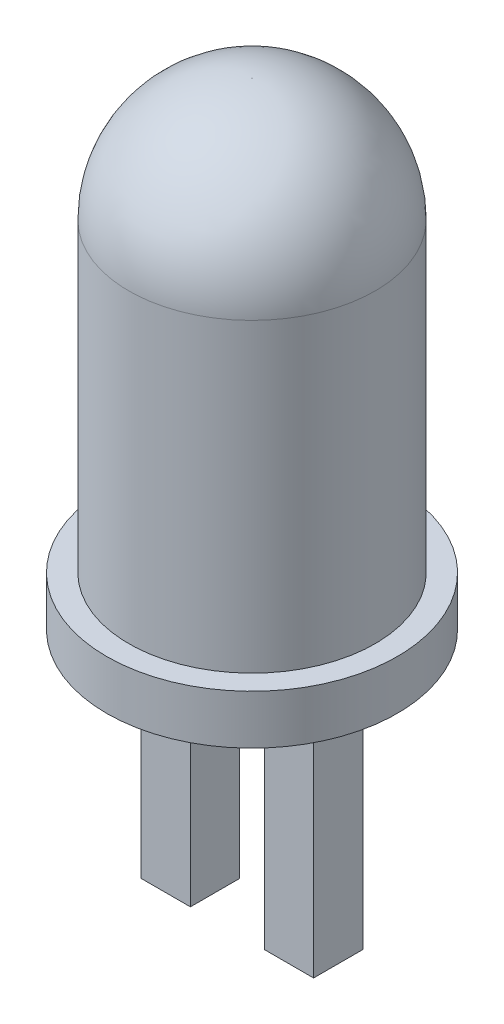
SolidWorks part; units mm, degrees
ref_plane "Front Plane" through (0, 0, 0) normal (0, 0, 1) x (1, 0, 0)
ref_plane "Top Plane" through (0, 0, 0) normal (0, 1, 0) x (1, 0, 0)
ref_plane "Right Plane" through (0, 0, 0) normal (1, 0, 0) x (0, 0, -1)
sketch "Sketch1" plane through (0, 0, 0) normal (1, 0, 0) x (0, 0, -1)
  line L0 (0, 0) -> (0, 9.69)
  line L1 (0, 0) -> (-2.95, 0)
  line L2 (-2.95, 0) -> (-2.95, 1)
  line L3 (-2.95, 1) -> (-2.5, 1)
  line L4 (-2.5, 1) -> (-2.5, 7.2)
  line L5 (-0.01, 9.69) -> (0, 9.69)
  arc A0 (-0.01, 9.69) -> (-2.5, 7.2) centre (-0.01, 7.2) ccw
  point P10 (-2.5, 9.69)
  dimension "D5" = 2.49
  dimension "D1" = 2.95
  dimension "D2" = 1
  dimension "D3" = 8.69
  dimension "D4" = 2.5
revolve "Revolve1" add sketch "Sketch1" angle 360 about L0
sketch "Sketch2" plane through (0, 0, 0) normal (0, -1, 0) x (1, 0, 0)
  line L1 (-1.75, -0.5) -> (-0.75, -0.5)
  line L2 (-1.75, -0.5) -> (-1.75, 0.5)
  line L3 (-1.75, 0.5) -> (-0.75, 0.5)
  line L4 (-0.75, -0.5) -> (-0.75, 0.5)
  line L5 (-1.75, -0.5) -> (-0.75, 0.5) construction
  line L6 (-1.75, 0.5) -> (-0.75, -0.5) construction
  line L7 (0.75, -0.5) -> (1.75, -0.5)
  line L8 (0.75, -0.5) -> (0.75, 0.5)
  line L9 (0.75, 0.5) -> (1.75, 0.5)
  line L10 (1.75, -0.5) -> (1.75, 0.5)
  line L11 (0.75, -0.5) -> (1.75, 0.5) construction
  line L12 (0.75, 0.5) -> (1.75, -0.5) construction
  point P0 (-1.25, 0)
  point P5 (1.25, 0)
  dimension "D1" = 1
  dimension "D2" = 1.5
  dimension "D3" = 0.75
extrude "Boss-Extrude1" add sketch "Sketch2" along normal blind 5
